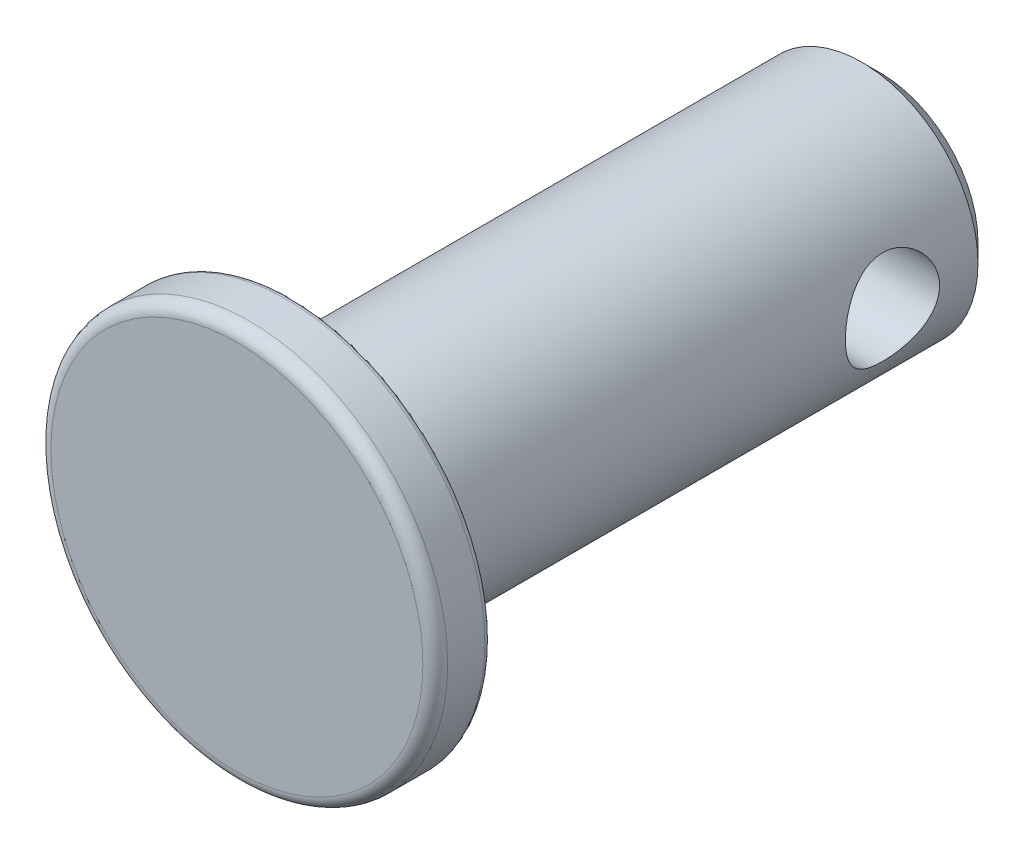
SolidWorks part; units mm, degrees
material "Alloy Steel"
ref_plane "Front Plane" through (0, 0, 0) normal (0, 0, 1) x (1, 0, 0)
ref_plane "Top Plane" through (0, 0, 0) normal (0, 1, 0) x (1, 0, 0)
ref_plane "Right Plane" through (0, 0, 0) normal (1, 0, 0) x (0, 0, -1)
sketch "Sketch1" plane through (0, 0, 0) normal (1, 0, 0) x (0, 0, -1)
  line L0 (0, 0) -> (84.6527, 0) construction
  line L1 (0, 0) -> (0, 3.81)
  line L2 (0.254, 4.064) -> (1.016, 4.064)
  line L3 (1.143, 3.937) -> (1.143, 2.3813)
  line L4 (1.143, 2.3813) -> (12.8016, 2.3813)
  line L5 (12.8016, 2.3813) -> (13.1826, 2.0003)
  line L6 (13.1826, 2.0003) -> (13.1826, 0)
  line L7 (13.1826, 0) -> (0, 0)
  arc A0 (0.254, 4.064) -> (0, 3.81) centre (0.254, 3.81) ccw
  arc A1 (1.143, 3.937) -> (1.016, 4.064) centre (1.016, 3.937) ccw
  point P11 (0, 4.064)
  dimension "D7" = 0.254
  dimension "D8" = 0.127
  dimension "D1" = 1.143
  dimension "D2" = 4.7625
  dimension "D3" = 8.128
  dimension "D4" = 13.1826
  dimension "D5" = 45
  dimension "D6" = 0.381
revolve "Revolve Base" add sketch "Sketch1" angle 360 about L0
sketch "Sketch2" plane through (0, 0, 0) normal (1, 0, 0) x (0, 0, -1)
  line L0 (0, 0) -> (11.049, 0) construction
  line L2 (13.1826, -2.0003) -> (13.1826, 2.0003) construction
  circle A0 centre (11.049, 0) radius 0.9652
  dimension "D1" = 1.9304
  dimension "D3" = 2.1336
extrude "Extrude1" cut sketch "Sketch2" against normal through all and the other way through all
